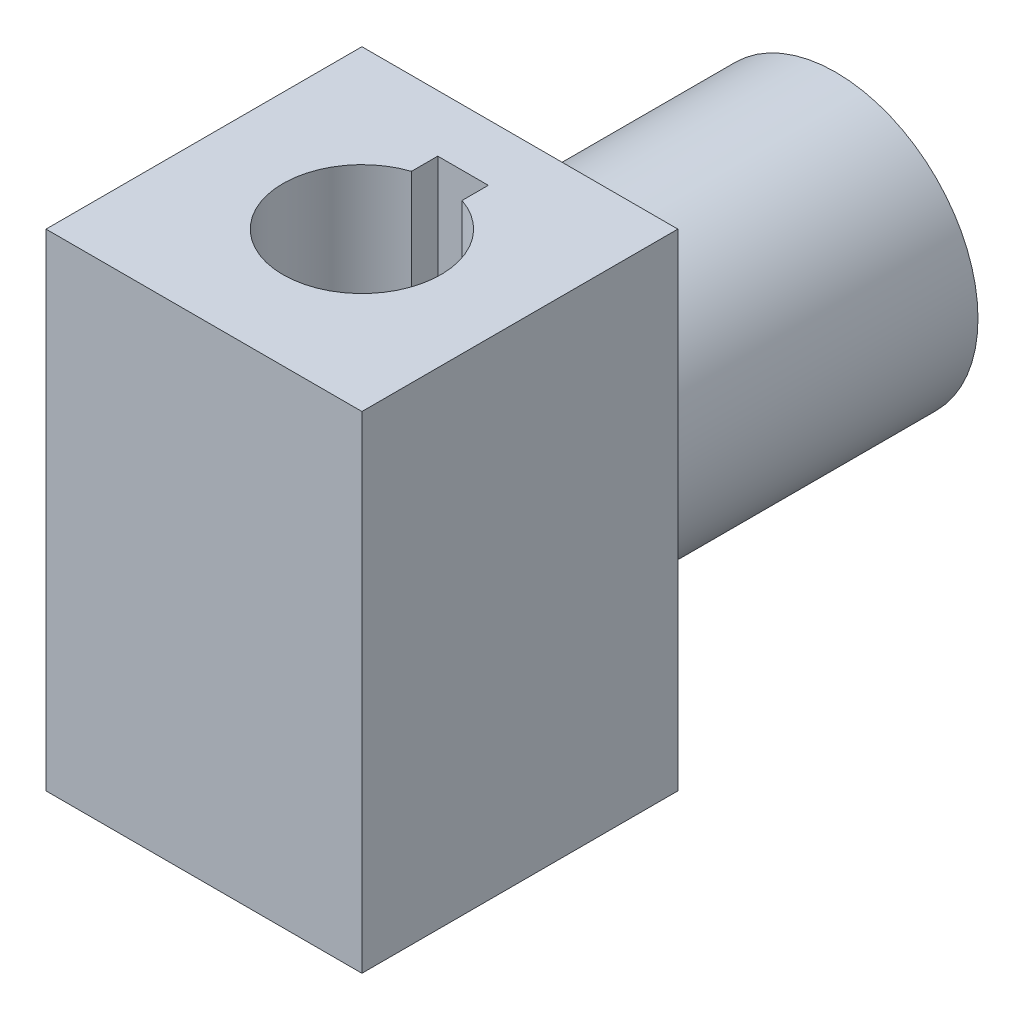
SolidWorks part; units mm, degrees
ref_plane "Front Plane" through (0, 0, 0) normal (0, 0, 1) x (1, 0, 0)
ref_plane "Top Plane" through (0, 0, 0) normal (0, 1, 0) x (1, 0, 0)
ref_plane "Right Plane" through (0, 0, 0) normal (1, 0, 0) x (0, 0, -1)
sketch "Sketch1" plane through (0, 0, 0) normal (0, 1, 0) x (1, 0, 0)
  line L1 (4, 9) -> (-4, 9)
  line L2 (4, 9) -> (4, 16)
  line L3 (4, 16) -> (-4, 16)
  line L4 (-4, 9) -> (-4, 16)
  line L5 (4, 9) -> (-4, 16) construction
  line L6 (4, 16) -> (-4, 9) construction
  line L7 (-25, -25) -> (25, -25)
  line L8 (-25, -25) -> (-25, 25)
  line L9 (-25, 25) -> (25, 25)
  line L10 (25, -25) -> (25, 25)
  line L11 (-25, -25) -> (25, 25) construction
  line L12 (-25, 25) -> (25, -25) construction
  circle A0 centre (0, 0) radius 12.5
  point P4 (0, 12.5)
  dimension "D1" = 25
  dimension "D2" = 50
  dimension "D3" = 7
  dimension "D4" = 8
  dimension "D5" = 50
extrude "Boss-Extrude1" add sketch "Sketch1" along normal blind 77 contours L7 L10 L9 L8 A0 L4 L3 L2
sketch "Sketch2" plane through (0, 0, -25) normal (0, 0, -1) x (-1, 0, 0)
  circle A0 centre (0, 38.5) radius 22.5
  dimension "D1" = 45
extrude "Boss-Extrude2" add sketch "Sketch2" along normal blind 50
